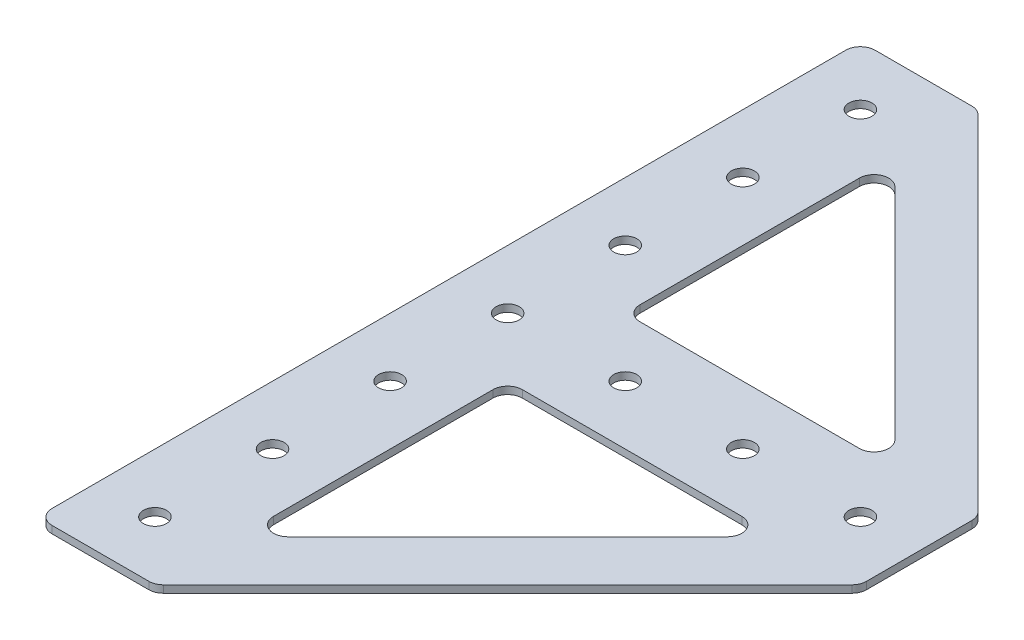
SolidWorks part; units mm, degrees
material "6061-T6 (SS)"
ref_plane "Front Plane" through (0, 0, 0) normal (0, 0, 1) x (1, 0, 0)
ref_plane "Top Plane" through (0, 0, 0) normal (0, 1, 0) x (1, 0, 0)
ref_plane "Right Plane" through (0, 0, 0) normal (1, 0, 0) x (0, 0, -1)
sketch "Sketch1" plane through (0, 0, 0) normal (0, 1, 0) x (1, 0, 0)
  line L0 (0, 0) -> (0, 177.8)
  line L3 (101.6, 88.9) -> (0, 88.9) construction
  line L4 (25.4, 0) -> (101.6, 76.2)
  line L5 (0, 177.8) -> (25.4, 177.8)
  line L6 (0, 177.8) -> (0, 0)
  line L7 (0, 0) -> (25.4, 0)
  line L8 (25.4, 159.8395) -> (25.4, 101.6)
  line L9 (25.4, 101.6) -> (83.6395, 101.6)
  line L11 (25.4, 76.2) -> (83.6395, 76.2)
  line L12 (101.6, 101.6) -> (101.6, 76.2)
  line L13 (101.6, 101.6) -> (25.4, 177.8)
  line L14 (25.4, 76.2) -> (25.4, 17.9605)
  line L15 (83.6395, 101.6) -> (25.4, 159.8395)
  line L16 (25.4, 17.9605) -> (83.6395, 76.2)
  line L17 (92.6197, 92.6197) -> (16.4197, 168.8197) construction
  line L18 (16.4197, 8.9803) -> (92.6197, 85.1803) construction
  line L19 (83.6395, 101.6) -> (83.6395, 76.2) construction
  point P9 (83.6395, 88.9)
  dimension "D1" = 177.8
  dimension "D2" = 101.6
  dimension "D3" = 25.4
  dimension "D5" = 25.4
  dimension "D6" = 12.7
  dimension "D7" = 12.7
extrude "Boss-Extrude1" add sketch "Sketch1" along normal blind 1.5875 contours L12 L13 L5 L0 L7 L4 L16 L14 L11 L15 L9 L8
hole_wizard "#9 (0.196) Diameter Hole1" positions "3DSketch1" profile "Sketch2" hole size "#9" standard "ANSI Inch" end condition through all
sketch3d "3DSketch1"
  line L0 (0, 1.5875, 0) -> (0, 1.5875, -177.8) construction
  line L1 (25.4, 1.5875, -101.6) -> (83.6395, 1.5875, -101.6) construction
  point P0 (12.7, 1.5875, -88.9)
  dimension "D1" = 12.7
  dimension "D2" = 12.7
sketch "Sketch2" plane through (12.7, 1.5875, -88.9) normal (1, 0, 0) x (0, 0, 1)
  line L0 (0, 0) -> (0, 1.5875)
  line L1 (0, 1.5875) -> (2.4892, 1.5875)
  line L2 (2.4892, 1.5875) -> (2.4892, 0)
  line L5 (2.4892, 0) -> (0, 0)
  line L11 (0, -6.35) -> (0, 107.95) construction
  dimension "Thru Hole Dia." = 4.9784
  dimension "Thru Hole Depth" = 1.5875
pattern_linear "LPattern1" count 4 spacing 25.4 along (0, 0, -1) count 4 spacing 25.4 along (1, 0, 0) of "#9 (0.196) Diameter Hole1"
pattern_linear "LPattern2" count 4 spacing 25.4 along (0, 0, 1) of "#9 (0.196) Diameter Hole1"
fillet "Fillet1" radius 3.175 12 edges at (101.6, 0.7937, -76.2) (0, 0.7937, 0) (0, 0.7937, -177.8) (25.4, 0.7937, -177.8) (101.6, 0.7937, -101.6) (25.4, 0.7937, -159.8395) (25.4, 0.7937, -101.6) (83.6395, 0.7937, -101.6) (83.6395, 0.7937, -76.2) (25.4, 0.7937, -76.2) (25.4, 0.7937, -17.9605) (25.4, 0.7937, 0)
